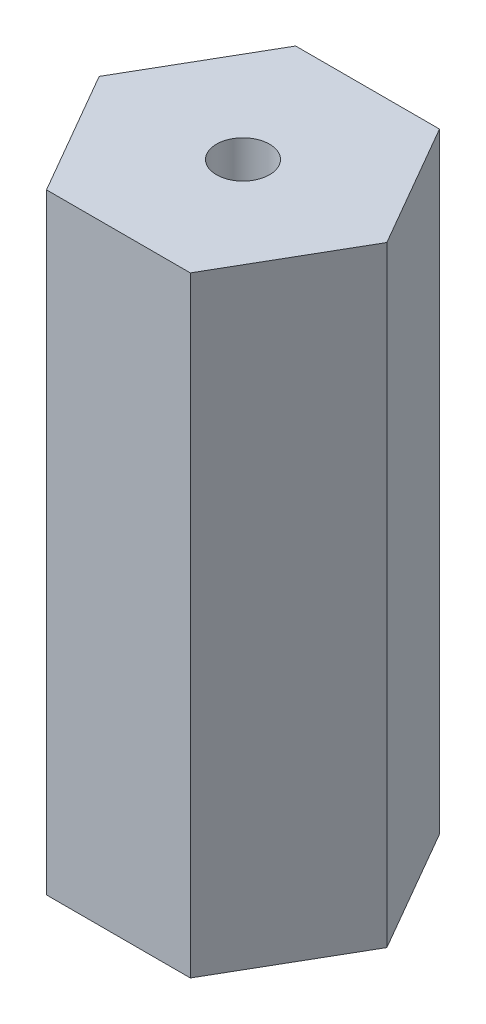
SolidWorks part; units mm, degrees
ref_plane "Front Plane" through (0, 0, 0) normal (0, 0, 1) x (1, 0, 0)
ref_plane "Top Plane" through (0, 0, 0) normal (0, 1, 0) x (1, 0, 0)
ref_plane "Right Plane" through (0, 0, 0) normal (1, 0, 0) x (0, 0, -1)
sketch "Sketch1" plane through (0, 0, 0) normal (0, 1, 0) x (1, 0, 0)
  line L1 (3.5218, 6.1) -> (-3.5218, 6.1)
  line L2 (-3.5218, 6.1) -> (-7.0437, 0)
  line L3 (-7.0437, 0) -> (-3.5218, -6.1)
  line L4 (-3.5218, -6.1) -> (3.5218, -6.1)
  line L5 (3.5218, -6.1) -> (7.0437, 0)
  line L6 (7.0437, 0) -> (3.5218, 6.1)
  circle A0 centre (0, 0) radius 6.1 construction
  dimension "D1" = 12.2
extrude "Boss-Extrude1" add sketch "Sketch1" along normal blind 29.9008
sketch "Sketch2" plane through (0, 29.9008, 0) normal (0, 1, 0) x (1, 0, 0)
  circle A0 centre (0, 0) radius 1.3
  dimension "D1" = 2.6
extrude "Cut-Extrude1" cut sketch "Sketch2" against normal through all
